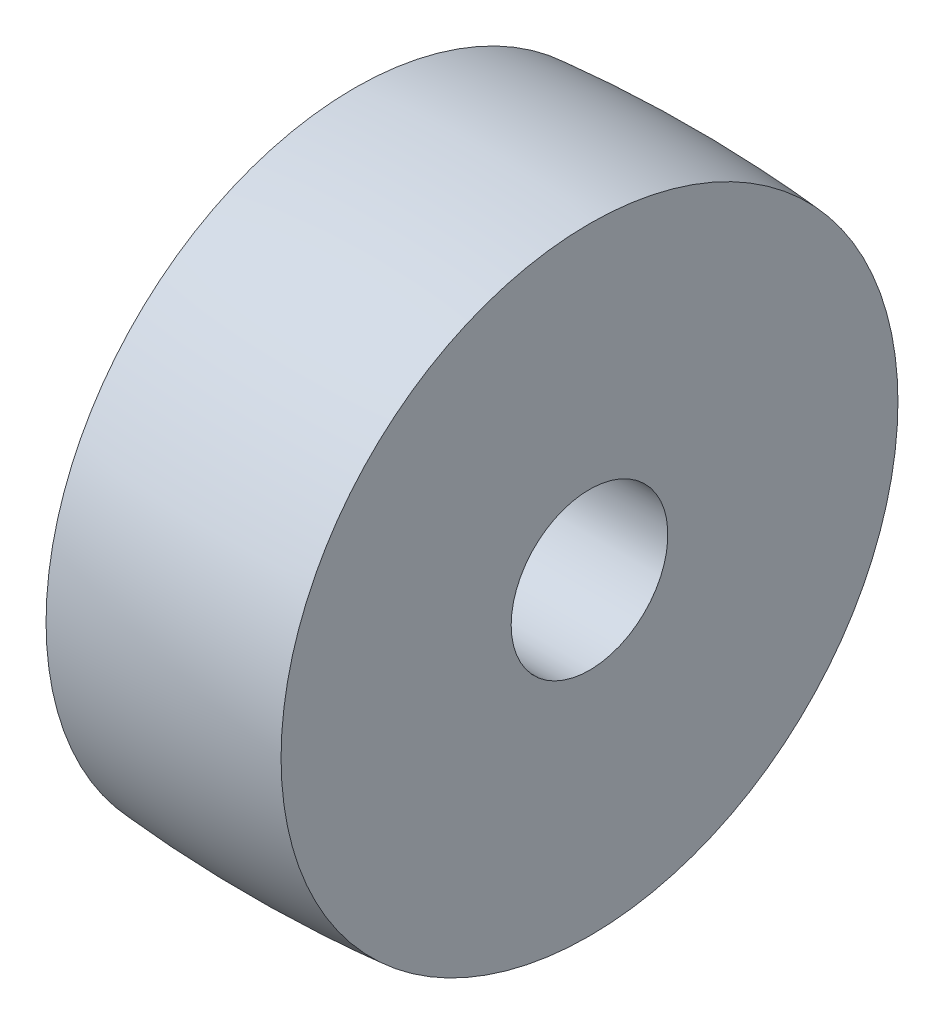
SolidWorks part; units mm, degrees
ref_plane "Front Plane" through (0, 0, 0) normal (0, 0, 1) x (1, 0, 0)
ref_plane "Top Plane" through (0, 0, 0) normal (0, 1, 0) x (1, 0, 0)
ref_plane "Right Plane" through (0, 0, 0) normal (1, 0, 0) x (0, 0, -1)
sketch "Sketch1" plane through (0, 0, 0) normal (0, 0, 1) x (1, 0, 0)
  line L0 (0, 0) -> (0, 25.4) construction
  line L1 (-38.1, 25.4) -> (38.1, 25.4)
  line L2 (-38.1, 25.4) -> (-38.1, 100.0125)
  line L3 (38.1, 25.4) -> (38.1, 100.0125)
  line L4 (0, 38.1) -> (0, 50038.1) construction
  arc A0 (-38.1, 100.0125) -> (38.1, 100.0125) centre (0, -356.3937) cw
  point P6 (0, 25.4)
  point P14 (0, 101.6)
  dimension "D1" = 25.4
  dimension "D2" = 76.2
  dimension "D3" = 76.2
  dimension "D4" = 1.5875
ref_axis "Axis1" through (-41.91, 0, 0) along (1, 0, 0)
revolve "Revolve1" add sketch "Sketch1" angle 360 about axis through (-41.91, 0, 0) along (1, 0, 0)
sketch "Sketch2" plane through (38.1, 0, 0) normal (1, 0, 0) x (0, 0, -1)
  line L0 (0, 0) -> (0, 93.6625) construction
  line L1 (0, 0) -> (93.6625, 0) construction
  line L2 (14.7123, 92.4998) -> (6.35, 84.1375)
  line L3 (6.35, 84.1375) -> (0, 84.1375)
  line L4 (18.5166, 91.8139) -> (6.9921, 80.2894)
  line L5 (0, 80.9625) -> (3.175, 80.9625)
  line L6 (6.9921, 80.2894) -> (11.1198, 71.4375)
  line L7 (3.175, 80.9625) -> (7.6166, 71.4375)
  line L8 (7.6166, 71.4375) -> (3.175, 61.9125)
  line L9 (3.175, 61.9125) -> (0, 61.9125)
  line L10 (11.1198, 71.4375) -> (5.5874, 59.5731)
  line L11 (5.5874, 59.5731) -> (12.1791, 51.4625)
  line L12 (12.1791, 51.4625) -> (8.4687, 46.3426)
  line L17 (0, 60.325) -> (3.175, 60.325)
  line L18 (3.175, 60.325) -> (0, 54.8257)
  line L19 (4.4223, 57.4151) -> (1.2955, 52.7433)
  line L20 (1.2955, 52.7433) -> (1.2955, 46.3426)
  line L21 (4.4223, 57.4151) -> (9.0205, 51.4625)
  line L22 (9.0205, 51.4625) -> (5.5874, 46.333)
  circle A0 centre (0, 0) radius 34.925
  circle A1 centre (0, 0) radius 93.6625
  circle A2 centre (0, 0) radius 100.0125 construction
  circle A3 centre (0, 0) radius 25.4 construction
  point P21 (1.5875, 80.9625)
  dimension "D1" = 6.35
  dimension "D2" = 9.525
  dimension "D3" = 6.35
  dimension "D4" = 135
  dimension "D5" = 9.525
  dimension "D6" = 3.175
  dimension "D7" = 3.175
  dimension "D8" = 115
  dimension "D9" = 3.175
  dimension "D10" = 3.175
  dimension "D11" = 3.175
  dimension "D12" = 19.05
  dimension "D13" = 1.5875
  dimension "D14" = 60
  dimension "D15" = 3.175
